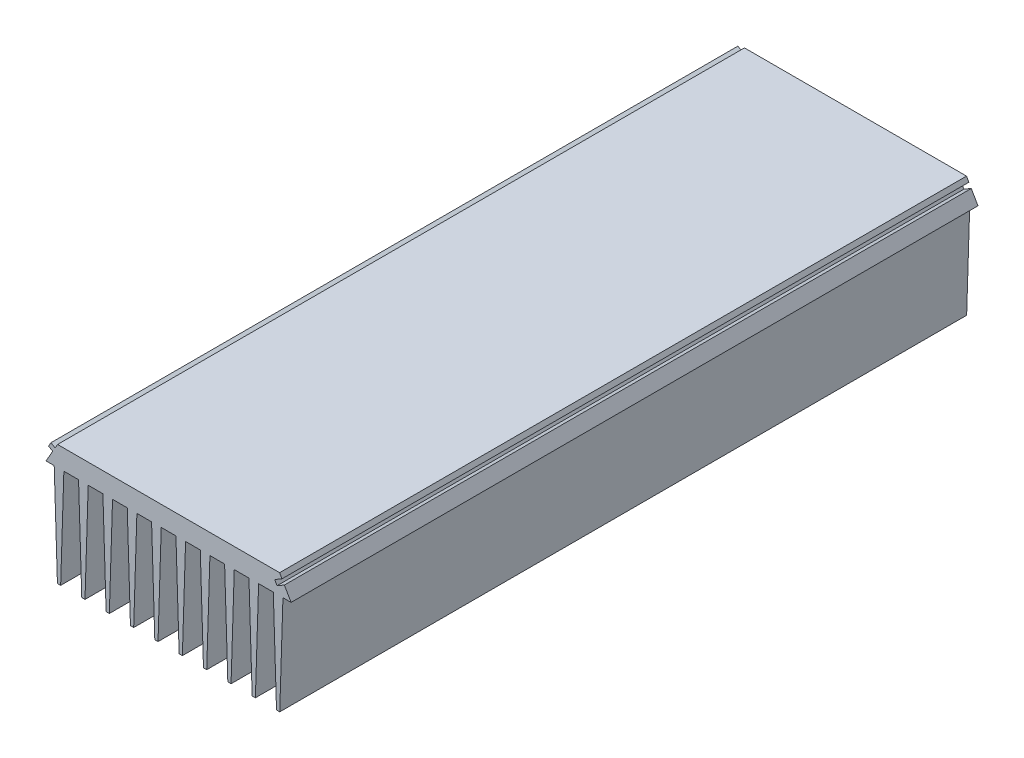
SolidWorks part; units mm, degrees
ref_plane "Plano frontal" through (0, 0, 0) normal (0, 0, 1) x (1, 0, 0)
ref_plane "Plano superior" through (0, 0, 0) normal (0, 1, 0) x (1, 0, 0)
ref_plane "Plano direito" through (0, 0, 0) normal (1, 0, 0) x (0, 0, -1)
sketch "Esboço1" plane through (0, 0, 0) normal (0, 0, 1) x (1, 0, 0)
  line L0 (0.1294, 0.0004) -> (0.1294, 50.0004)
  line L1 (0.1294, 50.0004) -> (115.2294, 50.0004)
  line L2 (115.2294, 50.0004) -> (115.2294, 0.0004)
  line L3 (0.1294, 0.0004) -> (115.2294, 0.0004) construction
  line L4 (0.1294, 41.7004) -> (4.1294, 41.7004) construction
  line L5 (4.1294, 41.7004) -> (10.2294, 41.7004)
  line L6 (10.2294, 41.7004) -> (14.2294, 41.7004) construction
  line L7 (14.2294, 41.7004) -> (20.3294, 41.7004)
  line L8 (20.3294, 41.7004) -> (24.3294, 41.7004) construction
  line L9 (24.3294, 41.7004) -> (30.4294, 41.7004)
  line L10 (30.4294, 41.7004) -> (34.4294, 41.7004) construction
  line L11 (34.4294, 41.7004) -> (40.5294, 41.7004)
  line L12 (40.5294, 41.7004) -> (44.5294, 41.7004) construction
  line L13 (44.5294, 41.7004) -> (50.6294, 41.7004)
  line L14 (50.6294, 41.7004) -> (54.6294, 41.7004) construction
  line L15 (54.6294, 41.7004) -> (60.7294, 41.7004)
  line L16 (60.7294, 41.7004) -> (64.7294, 41.7004) construction
  line L17 (64.7294, 41.7004) -> (70.8294, 41.7004)
  line L18 (70.8294, 41.7004) -> (74.8294, 41.7004) construction
  line L19 (74.8294, 41.7004) -> (80.9294, 41.7004)
  line L20 (80.9294, 41.7004) -> (84.9294, 41.7004) construction
  line L21 (84.9294, 41.7004) -> (91.0294, 41.7004)
  line L22 (91.0294, 41.7004) -> (95.0294, 41.7004) construction
  line L23 (95.0294, 41.7004) -> (101.1294, 41.7004)
  line L24 (101.1294, 41.7004) -> (105.1294, 41.7004) construction
  line L25 (105.1294, 41.7004) -> (111.2294, 41.7004)
  line L26 (111.2294, 41.7004) -> (115.2294, 41.7004) construction
  line L27 (4.1294, 41.7004) -> (2.8, 0.0004)
  line L28 (2.8, 0.0004) -> (0.1294, 0.0004)
  line L29 (10.2294, 41.7004) -> (11.5598, 0.0004)
  line L30 (11.5598, 0.0004) -> (12.9, 0.0004)
  line L31 (12.9, 0.0004) -> (14.2294, 41.7004)
  line L32 (20.3294, 41.7004) -> (21.6598, 0.0004)
  line L33 (21.6598, 0.0004) -> (23, 0.0004)
  line L34 (23, 0.0004) -> (24.3294, 41.7004)
  line L35 (30.4294, 41.7004) -> (31.7598, 0.0004)
  line L36 (31.7598, 0.0004) -> (33.1, 0.0004)
  line L37 (33.1, 0.0004) -> (34.4294, 41.7004)
  line L38 (44.5294, 41.7004) -> (43.2, 0.0004)
  line L39 (43.2, 0.0004) -> (41.8598, 0.0004)
  line L40 (41.8598, 0.0004) -> (40.5294, 41.7004)
  line L41 (54.6294, 41.7004) -> (53.3, 0.0004)
  line L42 (53.3, 0.0004) -> (51.9598, 0.0004)
  line L43 (51.9598, 0.0004) -> (50.6294, 41.7004)
  line L44 (64.7294, 41.7004) -> (63.4, 0.0004)
  line L45 (63.4, 0.0004) -> (62.0598, 0.0004)
  line L46 (62.0598, 0.0004) -> (60.7294, 41.7004)
  line L47 (74.8294, 41.7004) -> (73.5, 0.0004)
  line L48 (73.5, 0.0004) -> (72.1598, 0.0004)
  line L49 (72.1598, 0.0004) -> (70.8294, 41.7004)
  line L50 (84.9294, 41.7004) -> (83.6, 0.0004)
  line L51 (83.6, 0.0004) -> (82.2598, 0.0004)
  line L52 (82.2598, 0.0004) -> (80.9294, 41.7004)
  line L53 (95.0294, 41.7004) -> (93.7, 0.0004)
  line L54 (93.7, 0.0004) -> (92.3598, 0.0004)
  line L55 (92.3598, 0.0004) -> (91.0294, 41.7004)
  line L56 (101.1294, 41.7004) -> (102.4598, 0.0004)
  line L57 (102.4598, 0.0004) -> (103.8, 0.0004)
  line L58 (103.8, 0.0004) -> (105.1294, 41.7004)
  line L59 (111.2294, 41.7004) -> (112.5589, 0.0275)
  line L60 (112.5589, 0.0275) -> (115.2294, 0.0004)
  point P2 (2.8, 0.0004)
  dimension "D1" = 50
  dimension "D2" = 115.1
  dimension "D3" = 6.1
  dimension "D4" = 4
  dimension "D5" = 8.3
extrude "Ressalto-extrusão1" add sketch "Esboço1" along normal blind 285
sketch "Esboço2" plane through (0, 0, 0) normal (0, 0, -1) x (-1, 0, 0)
  line L0 (-104.7209, 48.2688) -> (-101.6898, 46.5188)
  line L1 (-101.6898, 46.5188) -> (-102.6898, 44.7867)
  line L2 (-102.6898, 44.7867) -> (-105.7209, 46.5367)
  line L3 (-105.7209, 46.5367) -> (-108.5131, 41.7004)
  line L4 (-105.1294, 41.7004) -> (-111.2294, 41.7004) construction
  line L5 (-108.917, 41.0008) -> (-105.7209, 46.5367) construction
  line L6 (-108.5131, 41.7004) -> (-108.5131, 0.0004)
  line L7 (-108.5131, 0.0004) -> (-115.2294, 0.0004)
  line L8 (-115.2294, 0.0004) -> (-115.2294, 50.0004)
  line L9 (-104.7209, 48.2688) -> (-103.7458, 50.0004)
  line L10 (-115.2294, 50.0004) -> (-0.1294, 50.0004) construction
  line L12 (-10.6132, 48.2688) -> (-8.8811, 49.2688)
  line L13 (-8.8811, 49.2688) -> (-7.8811, 47.5367)
  line L14 (-7.8811, 47.5367) -> (-9.6132, 46.5367)
  line L15 (-9.6132, 46.5367) -> (-6.8209, 41.7004)
  line L16 (-4.1294, 41.7004) -> (-10.2294, 41.7004) construction
  line L17 (-9.6132, 46.5367) -> (-6.417, 41.0008) construction
  line L18 (-6.8209, 41.7004) -> (-6.8209, 0)
  line L19 (-6.8209, 0) -> (0, 0)
  line L20 (0, 0) -> (-0.1294, 50.0004)
  line L21 (-0.1294, 50.0004) -> (-11.6129, 50.0004)
  line L22 (-11.6132, 50.0008) -> (-10.6132, 48.2688) construction
  line L23 (-11.6129, 50.0004) -> (-10.6132, 48.2688)
  line L24 (-103.7458, 50.0004) -> (-115.2294, 50.0004)
  line L25 (-57.6794, 50.0004) -> (-11.6129, 50.0004) construction
  line L26 (-57.6794, 50.0004) -> (-103.7458, 50.0004) construction
extrude "Corte-extrusão1" cut sketch "Esboço2" against normal through all both and the other way through all
